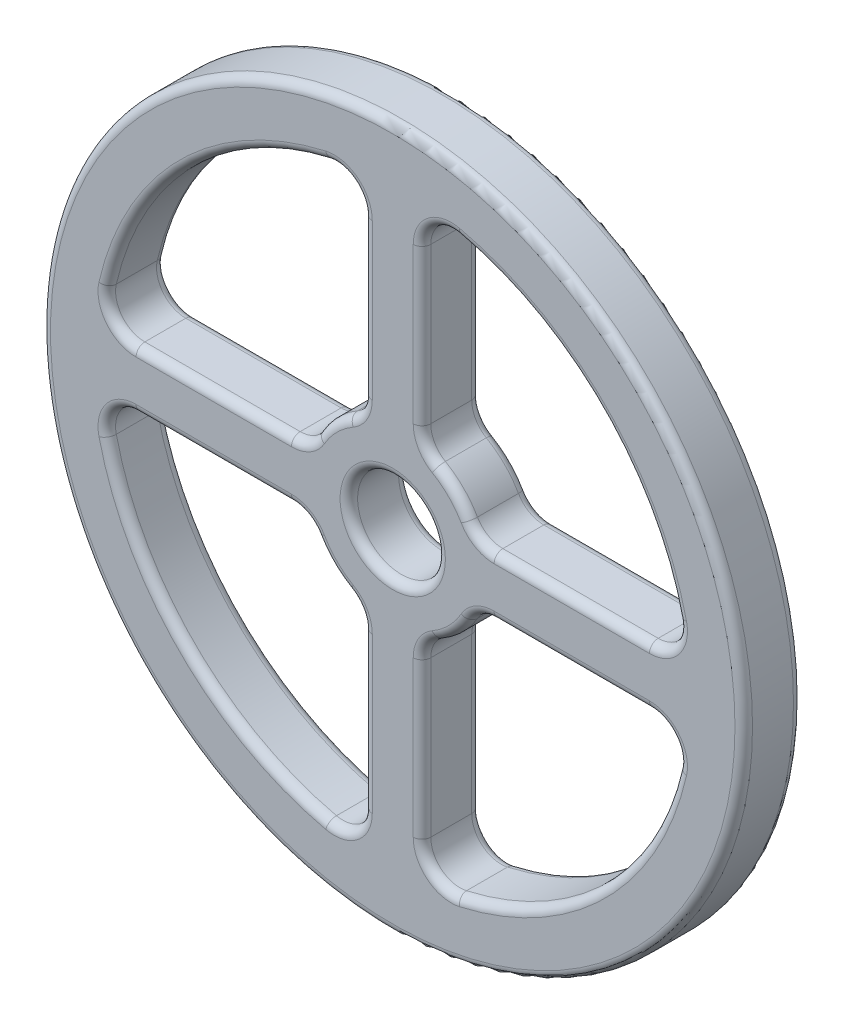
SolidWorks part; units mm, degrees
ref_plane "Front Plane" through (0, 0, 0) normal (0, 0, 1) x (1, 0, 0)
ref_plane "Top Plane" through (0, 0, 0) normal (0, 1, 0) x (1, 0, 0)
ref_plane "Right Plane" through (0, 0, 0) normal (1, 0, 0) x (0, 0, -1)
sketch "Sketch2" plane through (0, 0, 0) normal (0, 0, 1) x (1, 0, 0)
  circle A0 centre (0, 0) radius 120
  circle A1 centre (0, 0) radius 15
  dimension "D1" = 30
  dimension "D2" = 240
extrude "Boss-Extrude1" add sketch "Sketch2" along normal mid plane 20
sketch "Sketch3" plane through (0, 0, 10) normal (0, 0, 1) x (1, 0, 0)
  line L0 (0, 124.1816) -> (0, -156.4102) construction
  line L1 (-156.0908, 0) -> (224.7866, 0) construction
  line L2 (-10, -87.7496) -> (-10, -34.641)
  line L3 (-34.641, -10) -> (-87.7496, -10)
  line L4 (10, -87.7496) -> (10, -34.641)
  line L5 (34.641, -10) -> (87.7496, -10)
  line L6 (10, 87.7496) -> (10, 34.641)
  line L7 (34.641, 10) -> (87.7496, 10)
  line L8 (-34.641, 10) -> (-87.7496, 10)
  line L9 (-10, 87.7496) -> (-10, 34.641)
  arc A0 (-97.4996, -22.2222) -> (-22.2222, -97.4996) centre (0, 0) ccw
  arc A1 (22.2222, -97.4996) -> (97.4996, -22.2222) centre (0, 0) ccw
  arc A2 (97.4996, 22.2222) -> (22.2222, 97.4996) centre (0, 0) ccw
  arc A3 (-22.2222, 97.4996) -> (-97.4996, 22.2222) centre (0, 0) ccw
  arc A6 (-15, 25.9808) -> (-25.9808, 15) centre (0, 0) ccw
  arc A7 (15, 25.9808) -> (25.9808, 15) centre (0, 0) cw
  arc A8 (15, -25.9808) -> (25.9808, -15) centre (0, 0) ccw
  arc A9 (-15, -25.9808) -> (-25.9808, -15) centre (0, 0) cw
  arc A10 (-87.7496, -10) -> (-97.4996, -22.2222) centre (-87.7496, -20) ccw
  arc A11 (-15, -25.9808) -> (-10, -34.641) centre (-20, -34.641) cw
  arc A12 (-10, -87.7496) -> (-22.2222, -97.4996) centre (-20, -87.7496) cw
  arc A13 (87.7496, -10) -> (97.4996, -22.2222) centre (87.7496, -20) cw
  arc A14 (10, -87.7496) -> (22.2222, -97.4996) centre (20, -87.7496) ccw
  arc A15 (15, -25.9808) -> (10, -34.641) centre (20, -34.641) ccw
  arc A16 (25.9808, -15) -> (34.641, -10) centre (34.641, -20) cw
  arc A17 (10, 87.7496) -> (22.2222, 97.4996) centre (20, 87.7496) cw
  arc A18 (15, 25.9808) -> (10, 34.641) centre (20, 34.641) cw
  arc A19 (25.9808, 15) -> (34.641, 10) centre (34.641, 20) ccw
  arc A20 (87.7496, 10) -> (97.4996, 22.2222) centre (87.7496, 20) ccw
  arc A21 (-10, 87.7496) -> (-22.2222, 97.4996) centre (-20, 87.7496) ccw
  arc A22 (-87.7496, 10) -> (-97.4996, 22.2222) centre (-87.7496, 20) cw
  arc A23 (-15, 25.9808) -> (-10, 34.641) centre (-20, 34.641) ccw
  arc A24 (-34.641, 10) -> (-25.9808, 15) centre (-34.641, 20) ccw
  arc A25 (-25.9808, -15) -> (-34.641, -10) centre (-34.641, -20) ccw
  point P20 (0, 0)
  point P22 (0, 0)
  point P31 (-99.4987, -10)
  point P34 (-10, -28.2843)
  point P37 (-10, -99.4987)
  point P40 (99.4987, -10)
  point P43 (10, -99.4987)
  point P46 (10, -28.2843)
  point P49 (28.2843, -10)
  point P52 (10, 99.4987)
  point P55 (10, 28.2843)
  point P58 (28.2843, 10)
  point P61 (99.4987, 10)
  point P64 (-10, 99.4987)
  point P67 (-99.4987, 10)
  point P70 (-10, 28.2843)
  point P73 (-28.2843, 10)
  point P76 (-28.2843, -10)
  point P77 (0, 0)
  point P78 (0, 0)
  dimension "D1" = 200
  dimension "D4" = 30
  dimension "D5" = 10
  dimension "D6" = 10
  dimension "D2" = 10
  dimension "D3" = 10
extrude "Cut-Extrude1" cut sketch "Sketch3" against normal through all both and the other way through all
fillet "Fillet1" radius 3 68 edges at (-70.7107, -70.7107, 10) (-13.7639, -95.567, 10) (-10, -61.1953, 10) (-11.3397, -29.641, 10) (-21.2132, -21.2132, 10) (-29.641, -11.3397, 10) (-61.1953, -10, 10) (-95.567, -13.7639, 10) (61.1953, -10, 10) (29.641, -11.3397, 10) (21.2132, -21.2132, 10) (11.3397, -29.641, 10) (10, -61.1953, 10) (13.7639, -95.567, 10) (70.7107, -70.7107, 10) (95.567, -13.7639, 10) (10, 61.1953, 10) (11.3397, 29.641, 10) (21.2132, 21.2132, 10) (29.641, 11.3397, 10) (61.1953, 10, 10) (95.567, 13.7639, 10) (70.7107, 70.7107, 10) (13.7639, 95.567, 10) (-70.7107, 70.7107, 10) (-95.567, 13.7639, 10) (-61.1953, 10, 10) (-29.641, 11.3397, 10) (-21.2132, 21.2132, 10) (-11.3397, 29.641, 10) (-10, 61.1953, 10) (-13.7639, 95.567, 10) (-29.641, -11.3397, -10) (-21.2132, -21.2132, -10) (-11.3397, -29.641, -10) (-10, -61.1953, -10) (-13.7639, -95.567, -10) (-70.7107, -70.7107, -10) (-95.567, -13.7639, -10) (-61.1953, -10, -10) (13.7639, -95.567, -10) (10, -61.1953, -10) (11.3397, -29.641, -10) (21.2132, -21.2132, -10) (29.641, -11.3397, -10) (61.1953, -10, -10) (95.567, -13.7639, -10) (70.7107, -70.7107, -10) (95.567, 13.7639, -10) (61.1953, 10, -10) (29.641, 11.3397, -10) (21.2132, 21.2132, -10) (11.3397, 29.641, -10) (10, 61.1953, -10) (13.7639, 95.567, -10) (70.7107, 70.7107, -10) (-11.3397, 29.641, -10) (-21.2132, 21.2132, -10) (-29.641, 11.3397, -10) (-61.1953, 10, -10) (-95.567, 13.7639, -10) (-70.7107, 70.7107, -10) (-13.7639, 95.567, -10) (-10, 61.1953, -10) (120, 0, -10) (120, 0, 10) (15, 0, -10) (15, 0, 10)
